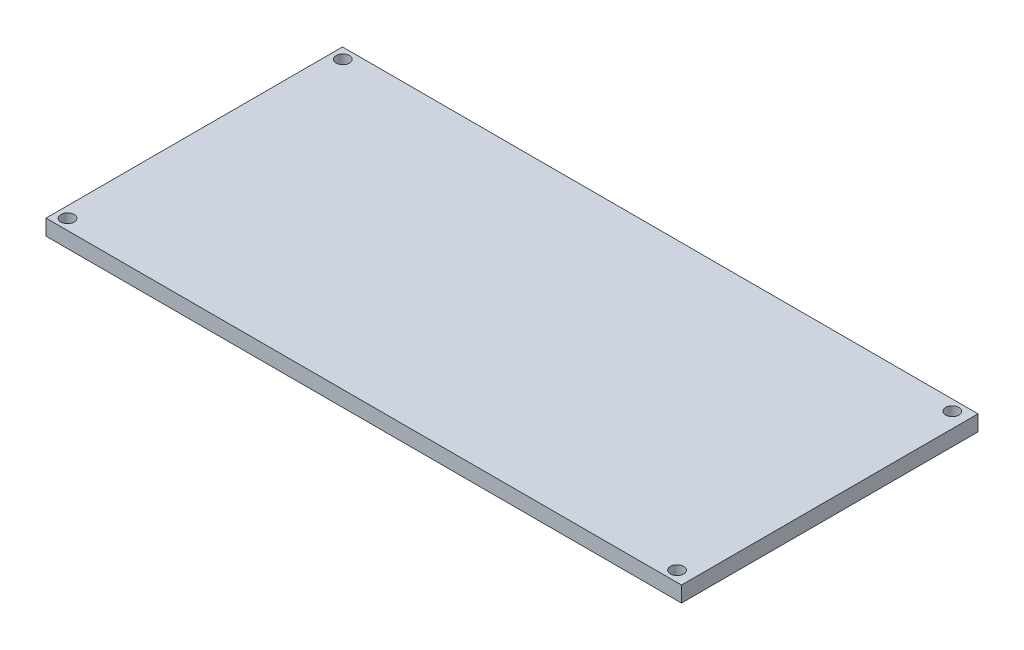
SolidWorks part; units mm, degrees
ref_plane "Front Plane" through (0, 0, 0) normal (0, 0, 1) x (1, 0, 0)
ref_plane "Top Plane" through (0, 0, 0) normal (0, 1, 0) x (1, 0, 0)
ref_plane "Right Plane" through (0, 0, 0) normal (1, 0, 0) x (0, 0, -1)
sketch "Sketch1" plane through (0, 0, 0) normal (0, 1, 0) x (1, 0, 0)
  line L1 (-56.86, 27.95) -> (62.95, 27.95)
  line L2 (-56.86, 27.95) -> (-56.86, -27.95)
  line L3 (-56.86, -27.95) -> (62.95, -27.95)
  line L4 (62.95, 27.95) -> (62.95, -27.95)
  point P4 (-56.86, 0)
  point P5 (62.95, 0)
  point P6 (3.045, 27.95)
  point P7 (3.045, -27.95)
  dimension "D1" = 119.81
  dimension "D2" = 55.9
extrude "Boss-Extrude1" add sketch "Sketch1" along normal blind 2.95
sketch "Sketch2" plane through (0, 2.95, 0) normal (0, 1, 0) x (1, 0, 0)
  line L0 (-56.86, -27.95) -> (62.95, -27.95) construction
  line L1 (62.95, 27.95) -> (-56.86, 27.95) construction
  line L2 (-56.86, 27.95) -> (-56.86, -27.95) construction
  line L3 (62.95, -27.95) -> (62.95, 27.95) construction
  circle A0 centre (-54.8021, -25.95) radius 1.25
  circle A1 centre (60.11, -25.95) radius 1.25
  circle A2 centre (-54.8021, 25.95) radius 1.25
  circle A3 centre (60.1079, 25.95) radius 1.25
  dimension "D1" = 2
  dimension "D4" = 2
  dimension "D5" = 2
  dimension "D6" = 2.84
  dimension "D7" = 2.8421
  dimension "D8" = 2.0579
  dimension "D2" = 2
  dimension "D3" = 2
extrude "Cut-Extrude1" cut sketch "Sketch2" against normal blind 10
